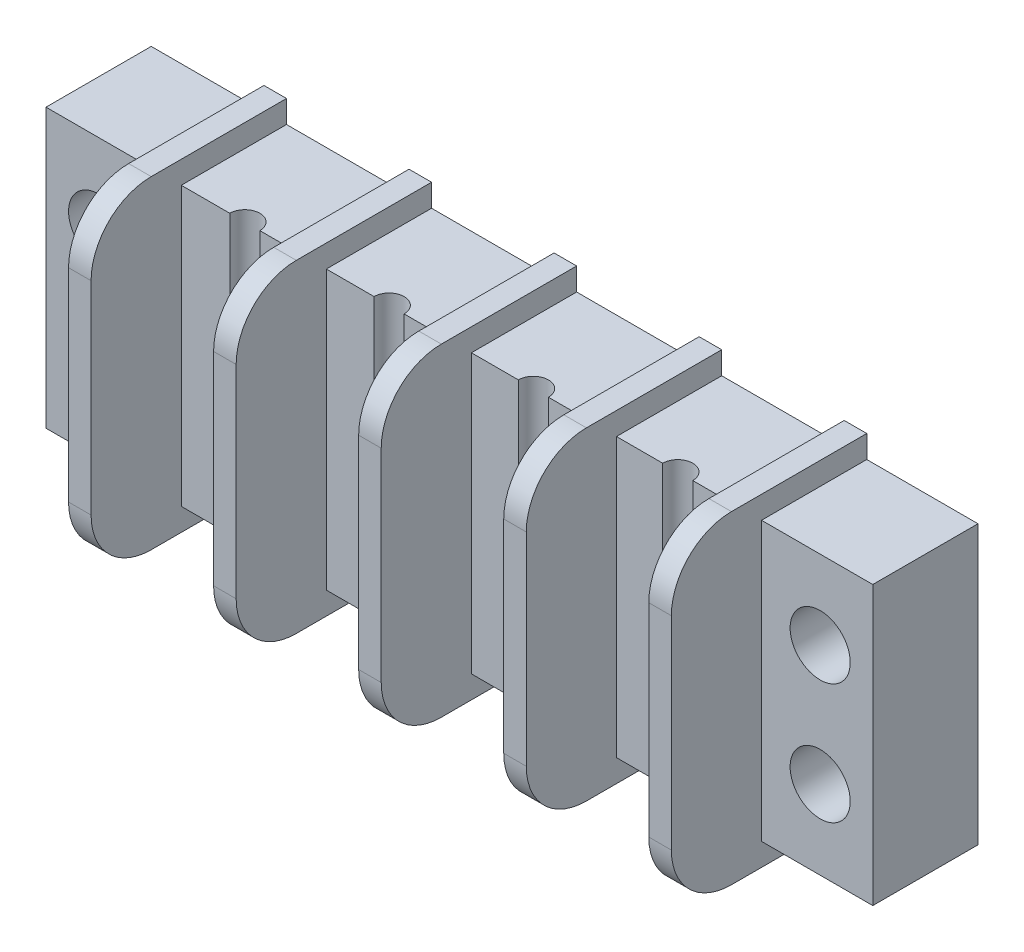
SolidWorks part; units mm, degrees
ref_plane "Plan de face" through (0, 0, 0) normal (0, 0, 1) x (1, 0, 0)
ref_plane "Plan de dessus" through (0, 0, 0) normal (0, 1, 0) x (1, 0, 0)
ref_plane "Plan de droite" through (0, 0, 0) normal (1, 0, 0) x (0, 0, -1)
sketch "Esquisse1" plane through (0, 0, 0) normal (0, 0, 1) x (1, 0, 0)
  line L1 (-29.2453, 13.0896) -> (25.7547, 13.0896)
  line L2 (-29.2453, 13.0896) -> (-29.2453, -5.4104)
  line L3 (-29.2453, -5.4104) -> (25.7547, -5.4104)
  line L4 (25.7547, 13.0896) -> (25.7547, -5.4104)
  dimension "D1" = 55
  dimension "D2" = 18.5
extrude "Boss.-Extru.1" add sketch "Esquisse1" along normal blind 7
sketch "Esquisse2" plane through (0, 0, 0) normal (0, 0, -1) x (-1, 0, 0)
  line L0 (-25.7547, 3.8396) -> (29.2453, 3.8396) construction
  line L1 (-25.7547, -5.4104) -> (-25.7547, 13.0896) construction
  line L2 (29.2453, 13.0896) -> (29.2453, -5.4104) construction
  line L3 (1.7453, 13.0896) -> (1.7453, -5.4104) construction
  line L4 (-25.7547, 13.0896) -> (29.2453, 13.0896) construction
  line L5 (29.2453, -5.4104) -> (-25.7547, -5.4104) construction
  circle A0 centre (-22.2547, 7.8396) radius 2
  circle A1 centre (-22.2547, -0.1604) radius 2
  circle A2 centre (25.7453, -0.1604) radius 2
  circle A3 centre (25.7453, 7.8396) radius 2
  dimension "D1" = 4
  dimension "D2" = 4
  dimension "D3" = 24
extrude "Enlèv. mat.-Extru.1" cut sketch "Esquisse2" against normal up to next
sketch "Esquisse3" plane through (0, 0, 0) normal (0, 0, -1) x (-1, 0, 0)
  line L0 (-25.7547, 3.8396) -> (29.2453, 3.8396) construction
  line L5 (-25.7547, -5.4104) -> (-25.7547, 13.0896) construction
  line L6 (29.2453, 13.0896) -> (29.2453, -5.4104) construction
  line L27 (20.2453, -6.9104) -> (20.2453, 14.5896)
  line L28 (20.2453, -6.9104) -> (21.7453, -6.9104)
  line L29 (21.7453, -6.9104) -> (21.7453, 14.5896)
  line L30 (20.2453, 14.5896) -> (21.7453, 14.5896)
  line L41 (29.2453, -5.4104) -> (-25.7547, -5.4104) construction
  line L42 (10.5953, -6.9104) -> (10.5953, 14.5896)
  line L43 (10.5953, 14.5896) -> (12.0953, 14.5896)
  line L44 (12.0953, -6.9104) -> (12.0953, 14.5896)
  line L45 (10.5953, -6.9104) -> (12.0953, -6.9104)
  line L46 (0.9453, -6.9104) -> (0.9453, 14.5896)
  line L47 (0.9453, 14.5896) -> (2.4453, 14.5896)
  line L48 (2.4453, -6.9104) -> (2.4453, 14.5896)
  line L49 (0.9453, -6.9104) -> (2.4453, -6.9104)
  line L50 (-8.7047, -6.9104) -> (-8.7047, 14.5896)
  line L51 (-8.7047, 14.5896) -> (-7.2047, 14.5896)
  line L52 (-7.2047, -6.9104) -> (-7.2047, 14.5896)
  line L53 (-8.7047, -6.9104) -> (-7.2047, -6.9104)
  line L54 (-18.3547, -6.9104) -> (-18.3547, 14.5896)
  line L55 (-18.3547, 14.5896) -> (-16.8547, 14.5896)
  line L56 (-16.8547, -6.9104) -> (-16.8547, 14.5896)
  line L57 (-18.3547, -6.9104) -> (-16.8547, -6.9104)
  dimension "D1" = 1.5
  dimension "D2" = 1.5
  dimension "D3" = 21.5
  dimension "D4" = 21.5
  dimension "D5" = 5
  dimension "D6" = 7.5
extrude "Boss.-Extru.2" add sketch "Esquisse3" against normal blind 13
fillet "Congé1" radius 4 10 edges at (-20.9953, -6.9104, 13) (-20.9953, 14.5896, 13) (-11.3453, -6.9104, 13) (-1.6953, -6.9104, 13) (7.9547, -6.9104, 13) (17.6047, -6.9104, 13) (17.6047, 14.5896, 13) (7.9547, 14.5896, 13) (-1.6953, 14.5896, 13) (-11.3453, 14.5896, 13)
sketch "Esquisse4" plane through (0, -5.4104, 0) normal (0, -1, 0) x (1, 0, 0)
  line L0 (8.7047, 7) -> (16.8547, 7) construction
  circle A0 centre (12.7797, 7) radius 1
  dimension "D1" = 2
extrude "Enlèv. mat.-Extru.2" cut sketch "Esquisse4" against normal up to next (18.5 mm away)
pattern_linear "Répétition linéaire1" count 4 spacing 9.6 along (-1, 0, 0) of "Enlèv. mat.-Extru.2"
